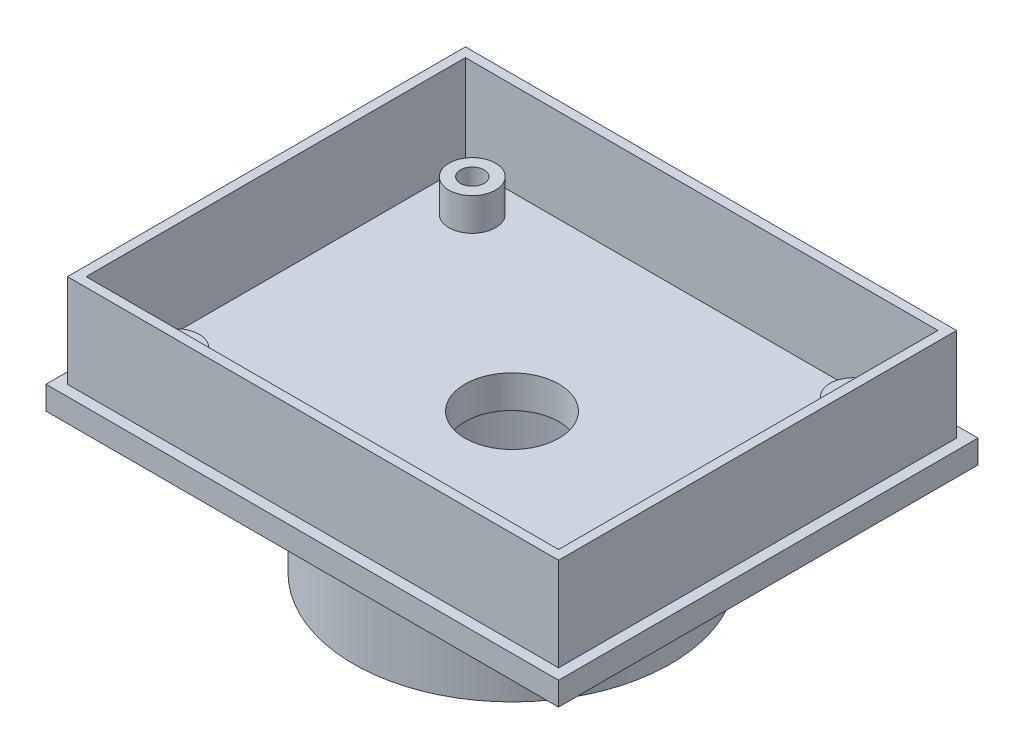
SolidWorks part; units mm, degrees
ref_plane "Front Plane" through (0, 0, 0) normal (0, 0, 1) x (1, 0, 0)
ref_plane "Top Plane" through (0, 0, 0) normal (0, 1, 0) x (1, 0, 0)
ref_plane "Right Plane" through (0, 0, 0) normal (1, 0, 0) x (0, 0, -1)
sketch "Sketch1" plane through (0, 0, 0) normal (0, 1, 0) x (1, 0, 0)
  line L1 (55, 45) -> (-55, 45)
  line L2 (55, 45) -> (55, -45)
  line L3 (55, -45) -> (-55, -45)
  line L4 (-55, 45) -> (-55, -45)
  line L5 (55, 45) -> (-55, -45) construction
  line L6 (55, -45) -> (-55, 45) construction
  point P0 (0, 0)
  dimension "D1" = 90
  dimension "D2" = 110
extrude "Boss-Extrude1" add sketch "Sketch1" along normal blind 5 contours L4 L3 L2 L1
sketch "Sketch4" plane through (0, 5, 0) normal (0, 1, 0) x (1, 0, 0)
  line L4 (-50.7, 40.7) -> (-50.7, -40.7)
  line L5 (-50.7, -40.7) -> (50.7, -40.7)
  line L6 (50.7, -40.7) -> (50.7, 40.7)
  line L7 (50.7, 40.7) -> (-50.7, 40.7)
  line L8 (52.7, 42.7) -> (-52.7, 42.7)
  line L9 (-52.7, 42.7) -> (-52.7, -42.7)
  line L10 (-52.7, -42.7) -> (52.7, -42.7)
  line L11 (52.7, -42.7) -> (52.7, 42.7)
  line L12 (52.7, 42.7) -> (-52.7, 42.7)
  line L13 (-52.7, 42.7) -> (-52.7, -42.7)
  line L14 (-52.7, -42.7) -> (52.7, -42.7)
  line L15 (52.7, -42.7) -> (52.7, 42.7)
  dimension "D1" = 2.3
  dimension "D2" = 2
extrude "Boss-Extrude2" add sketch "Sketch4" along normal blind 20
sketch "Sketch5" plane through (0, 5, 0) normal (0, 1, 0) x (1, 0, 0)
  circle A0 centre (-40.8469, 32.319) radius 5
  circle A1 centre (-40.8469, -31.281) radius 5
  circle A2 centre (40.9531, -31.2734) radius 5
  circle A3 centre (40.9531, 32.319) radius 5
  point P8 (39.6197, 32.3418)
  point P9 (39.6197, 28.2814)
  point P10 (-40.3803, 32.3418)
  point P11 (-40.3803, 28.2814)
  point P12 (-40.3803, -27.1462)
  point P13 (0, 0)
  point P14 (32.8902, -24.3456)
  point P15 (-30.7098, 23.5095)
  point P16 (-42.2143, -32.3336)
  point P17 (39.6197, -32.3391)
  point P18 (-40.7212, -29.4967)
  point P19 (40.9531, -29.4785)
  point P20 (-40.8469, 32.319)
  point P21 (40.9531, 32.319)
  point P22 (40.9531, -31.281)
  point P23 (40.9531, 32.319)
  dimension "D1" = 81.8
  dimension "D2" = 63.6
extrude "Boss-Extrude3" add sketch "Sketch5" along normal blind 7
sketch "Sketch9" plane through (0, 12, 0) normal (0, 1, 0) x (1, 0, 0)
  circle A0 centre (40.9531, 32.319) radius 2.5248
  circle A1 centre (40.9531, -31.2734) radius 2.5248
  circle A2 centre (-40.8469, -31.2734) radius 2.5248
  circle A3 centre (-40.8469, 32.319) radius 2.5248
  point P10 (40.9531, 32.319)
  point P11 (-40.8469, -31.2734)
extrude "Cut-Extrude1" cut sketch "Sketch9" against normal blind 5
sketch "Sketch10" plane through (0, 0, 0) normal (0, -1, 0) x (1, 0, 0)
  circle A0 centre (0, 0) radius 34
extrude "Boss-Extrude4" add sketch "Sketch10" along normal blind 25
sketch "Sketch11" plane through (0, -25, 0) normal (0, -1, 0) x (-1, 0, 0)
  circle A0 centre (0, 0) radius 10.0803
extrude "Cut-Extrude2" cut sketch "Sketch11" against normal blind 31
sketch3d "3DSketch1"
  spline S0 degree 3 poles (-8.1304, -25, -31.3073) (0.089, -25, -32.3578) (8.3999, -25, -31.2607) (16.2241, -25, -28.0102) (22.9367, -25, -22.8405) (28.0782, -25, -16.1062) (31.2957, -25, -8.2683) (32.3694, -25, 0.1361) (31.225, -25, 8.5311) (27.9418, -25, 16.3417) (22.7439, -25, 23.0325) (15.988, -25, 28.1457) (8.1366, -25, 31.3301) (-0.2721, -25, 32.3685) (-8.6623, -25, 31.1889) (-16.459, -25, 27.8729) (-23.1279, -25, 22.6469) (-28.2126, -25, 15.8696) (-31.3641, -25, 8.0049) (-32.3671, -25, -0.4082) (-31.1522, -25, -8.7933) (-27.8034, -25, -16.5761) (-22.5496, -25, -23.2229) (-15.8224, -25, -28.2257) (-8.1304, -25, -31.3073) (0.089, -25, -32.3578) (8.3999, -25, -31.2607) knots -0.122671 -0.080894 -0.040443 0 0.041778 0.083555 0.125333 0.16711 0.208888 0.250665 0.292443 0.334221 0.375998 0.417776 0.459553 0.501331 0.543108 0.584886 0.626663 0.668441 0.710219 0.751996 0.793774 0.835551 0.877329 0.919106 0.959557 1 1.041778 1.083555 1.125333 only from (0, -25, -32) to (0, -25, -32)
  spline S1 degree 3 poles (-8.1304, -25, -31.3073) (0.089, -25, -32.3578) (8.3999, -25, -31.2607) (16.2241, -25, -28.0102) (22.9367, -25, -22.8405) (28.0782, -25, -16.1062) (31.2957, -25, -8.2683) (32.3694, -25, 0.1361) (31.225, -25, 8.5311) (27.9418, -25, 16.3417) (22.7439, -25, 23.0325) (15.988, -25, 28.1457) (8.1366, -25, 31.3301) (-0.2721, -25, 32.3685) (-8.6623, -25, 31.1889) (-16.459, -25, 27.8729) (-23.1279, -25, 22.6469) (-28.2126, -25, 15.8696) (-31.3641, -25, 8.0049) (-32.3671, -25, -0.4082) (-31.1522, -25, -8.7933) (-27.8034, -25, -16.5761) (-22.5496, -25, -23.2229) (-15.8224, -25, -28.2257) (-8.1304, -25, -31.3073) (0.089, -25, -32.3578) (8.3999, -25, -31.2607) knots -0.122671 -0.080894 -0.040443 0 0.041778 0.083555 0.125333 0.16711 0.208888 0.250665 0.292443 0.334221 0.375998 0.417776 0.459553 0.501331 0.543108 0.584886 0.626663 0.668441 0.710219 0.751996 0.793774 0.835551 0.877329 0.919106 0.959557 1 1.041778 1.083555 1.125333 only from (0, -25, -32) to (0, -25, -32)
  dimension "D1" = 2
extrude "Cut-Extrude3" cut sketch "3DSketch1" along direction (0, -1, 0) on the side of the normal blind 23
sketch "Sketch12" plane through (0, 0, 0) normal (0, -1, 0) x (-1, 0, 0)
  circle A0 centre (0, 0) radius 40.8127 construction
